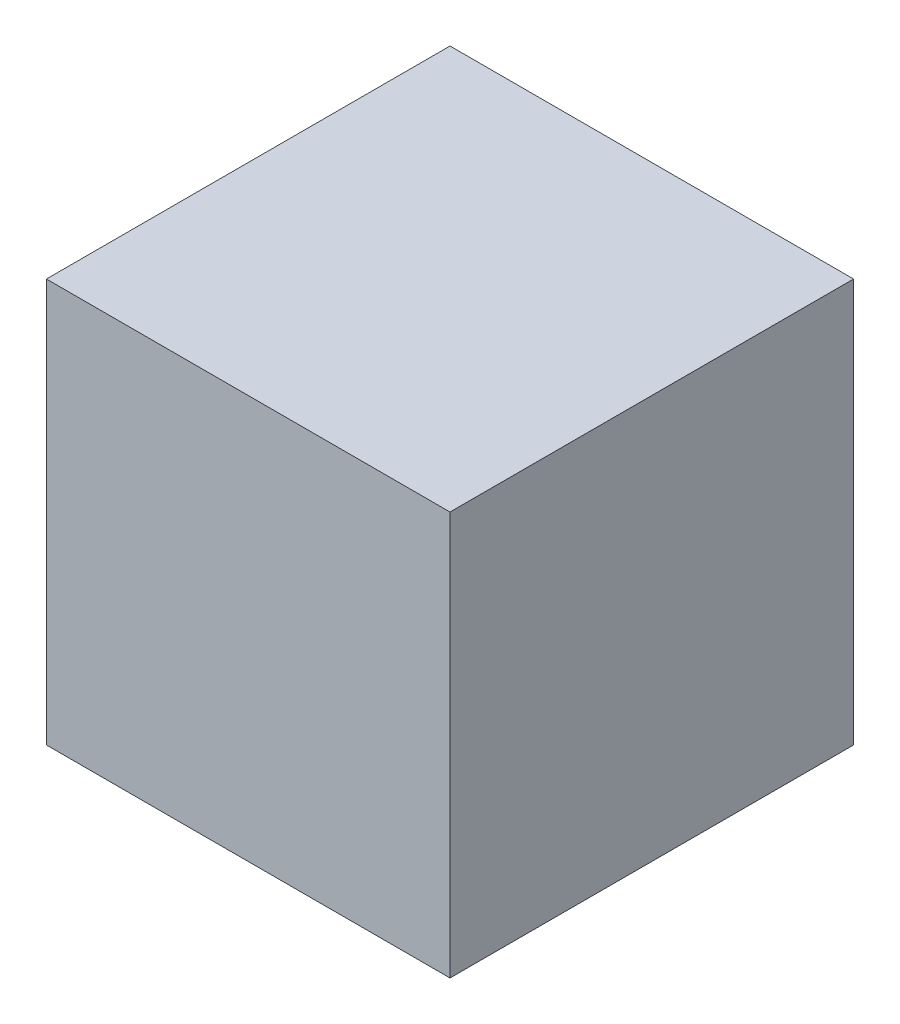
SolidWorks part; units mm, degrees
ref_plane "Plano frontal" through (0, 0, 0) normal (0, 0, 1) x (1, 0, 0)
ref_plane "Plano superior" through (0, 0, 0) normal (0, 1, 0) x (1, 0, 0)
ref_plane "Plano direito" through (0, 0, 0) normal (1, 0, 0) x (0, 0, -1)
sketch "Esboço1" plane through (0, 0, 0) normal (0, 0, 1) x (1, 0, 0)
  line L1 (-120.415, 120.415) -> (120.415, 120.415)
  line L2 (-120.415, 120.415) -> (-120.415, -120.415)
  line L3 (-120.415, -120.415) -> (120.415, -120.415)
  line L4 (120.415, 120.415) -> (120.415, -120.415)
  line L5 (-120.415, 120.415) -> (120.415, -120.415) construction
  line L6 (-120.415, -120.415) -> (120.415, 120.415) construction
  point P0 (0, 0)
  dimension "D1" = 240.83
  dimension "D2" = 240.83
extrude "Ressalto-extrusão1" add sketch "Esboço1" along normal mid plane 240.83
